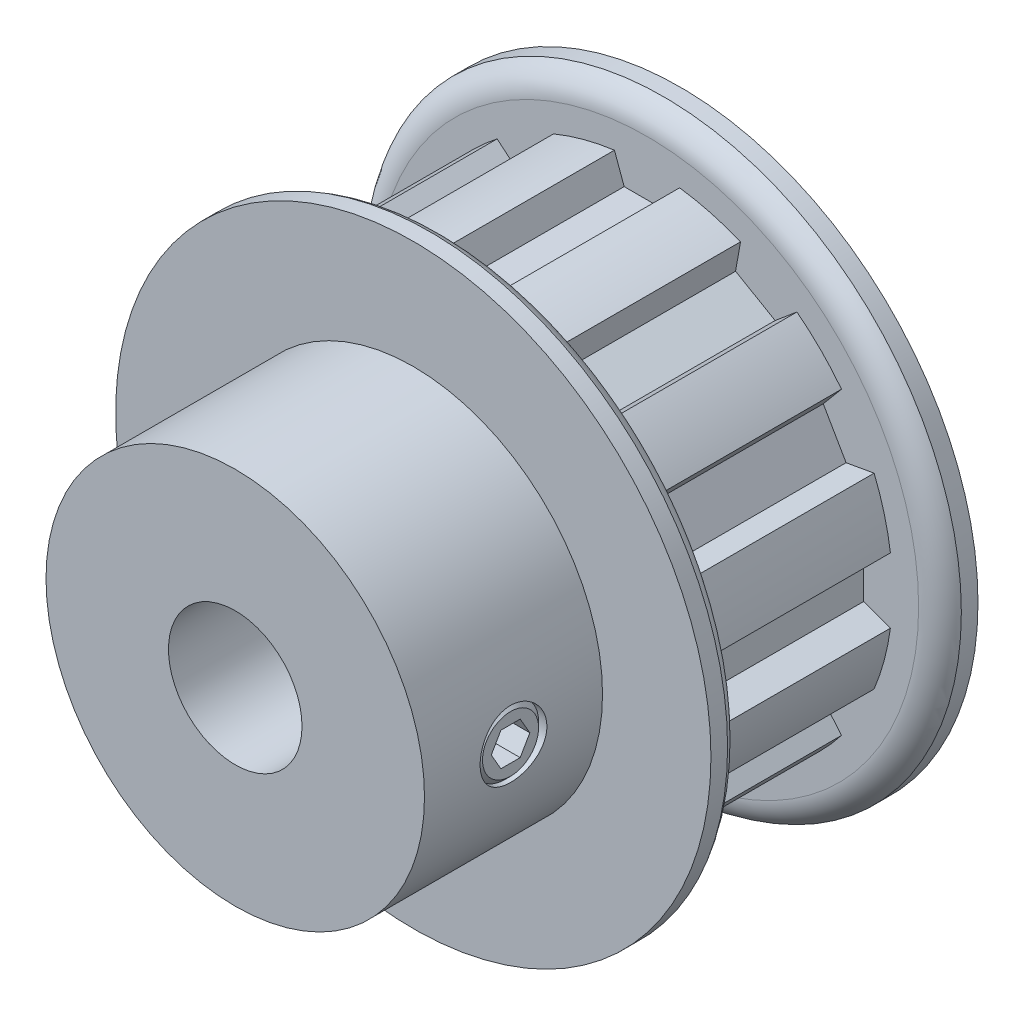
SolidWorks part; units mm, degrees
ref_plane "Front Plane" through (0, 0, 0) normal (0, 0, 1) x (1, 0, 0)
ref_plane "Top Plane" through (0, 0, 0) normal (0, 1, 0) x (1, 0, 0)
ref_plane "Right Plane" through (0, 0, 0) normal (1, 0, 0) x (0, 0, -1)
sketch "Sketch1" plane through (0, 0, 0) normal (0, 0, 1) x (1, 0, 0)
  line L0 (-2.3241, 17.3609) -> (-1.6307, 15.4559)
  line L1 (-1.6307, 15.4559) -> (1.6307, 15.4559)
  line L2 (1.6307, 15.4559) -> (2.3241, 17.3609)
  line L3 (-2.3241, 17.3609) -> (2.3241, 17.3609)
  line L4 (0, 0) -> (0, 15.4559) construction
  line L5 (0, 15.4559) -> (0, 19.0119) construction
  circle A0 centre (0, 0) radius 18.1864 construction
  circle A1 centre (0, 0) radius 21.2344 construction
  circle A2 centre (0, 0) radius 17.5158 construction
  point P6 (0, 17.3609)
  point P11 (0, 18.1864)
  point P13 (0, 21.2344)
  point P14 (0, 17.5158)
  dimension "D1" = 1.651
  dimension "D2" = 0.8255
sketch "Sketch2" plane through (0, 0, 0) normal (1, 0, 0) x (0, 0, -1)
  line L0 (-15.875, 4.7625) -> (15.875, 4.7625)
  line L1 (-15.875, 4.7625) -> (-15.875, 13.5001)
  line L2 (-15.875, 13.5001) -> (-3.175, 13.5001)
  line L3 (-3.175, 13.5001) -> (-3.175, 21.2344)
  line L4 (-3.175, 21.2344) -> (-0.8001, 21.2344) construction
  line L5 (-0.8001, 21.2344) -> (-0.8001, 17.5158) construction
  line L6 (-0.8001, 17.5158) -> (13.5001, 17.5158)
  line L7 (13.5001, 17.5158) -> (13.5001, 21.2344) construction
  line L8 (13.5001, 21.2344) -> (15.875, 21.2344) construction
  line L9 (15.875, 21.2344) -> (15.875, 4.7625)
  line L10 (-15.875, 0) -> (15.875, 0) construction
  line L13 (-3.175, 21.2344) -> (-1.9876, 21.2344)
  line L14 (-0.8001, 19.3751) -> (-0.8001, 17.5158)
  line L15 (13.5001, 17.5158) -> (13.5001, 19.3751)
  line L16 (14.6875, 21.2344) -> (15.875, 21.2344)
  arc A0 (-0.8001, 19.3751) -> (-1.9876, 21.2344) centre (-2.8495, 19.3751) ccw
  arc A1 (13.5001, 19.3751) -> (14.6875, 21.2344) centre (15.5495, 19.3751) cw
  point P12 (-0.8001, 19.3751)
  point P14 (-1.9876, 21.2344)
  point P20 (13.5001, 19.3751)
  point P21 (14.6875, 21.2344)
  point P25 (13.5001, 0)
  point P26 (-0.8001, 0)
  dimension "Bore" = 9.525
  dimension "Hub Dia" = 27.0002
  dimension "Outside Width" = 19.05
  dimension "Inside Width" = 14.3002
revolve "Revolve1" add sketch "Sketch2" angle 360 mid plane about L10
sketch "Sketch3" plane through (0, 0, 0) normal (0, 0, 1) x (1, 0, 0)
  line L0 (-1.6307, 15.4559) -> (1.6307, 15.4559) construction
  line L1 (1.6307, 15.4559) -> (2.3241, 17.3609) construction
  line L2 (-2.3241, 17.3609) -> (-1.6307, 15.4559) construction
  line L3 (-1.6307, 15.4559) -> (1.6307, 15.4559)
  line L4 (1.6307, 15.4559) -> (2.3241, 17.3609)
  line L5 (-2.3241, 17.3609) -> (-1.6307, 15.4559)
  circle A0 centre (0, 0) radius 17.5158 construction
  arc A1 (2.3241, 17.3609) -> (-2.3241, 17.3609) centre (0, 0) ccw
extrude "Cut-Extrude1" cut sketch "Sketch3" against normal up to vertex (13.5001 mm away) from vertex at 0.8001 starting at point (0, 17.5158, 0.8001)
pattern_circular "CirPattern1" count 12 over 360 about axis through (0, 0, 0) along (0, 0, 1) of "Cut-Extrude1"
sketch "Sketch4" plane through (0, 0, 0) normal (1, 0, 0) x (0, -1, 0)
  line L0 (0, -3.175) -> (0, -15.875) construction
  line L1 (-13.5001, -3.175) -> (13.5001, -3.175) construction
  line L2 (-13.5001, -15.875) -> (13.5001, -15.875) construction
  circle A0 centre (0, -9.525) radius 2.3813
  dimension "D1" = 4.7625
extrude "Cut-Extrude2" cut sketch "Sketch4" along normal through all
ref_plane "Plane1" through (0, 0, 9.525) normal (0, 0, 1) x (1, 0, 0)
sketch "Sketch5" plane through (0, 0, 9.525) normal (0, 0, 1) x (1, 0, 0)
  line L0 (0, 0.1664) -> (0, 13.5001) construction
  line L1 (4.7625, -2.0003) -> (4.7625, 0)
  line L2 (5.1435, -2.3813) -> (12.9074, -2.3813)
  line L3 (4.7625, 0) -> (13.5001, 0) construction
  line L4 (4.7625, 0) -> (13.2884, 0)
  line L5 (13.2884, 0) -> (13.2884, -2.0003)
  line L6 (5.1435, -2.3813) -> (4.7625, -2.0003)
  line L7 (13.2884, -2.0003) -> (12.9074, -2.3813)
  circle A0 centre (0, 0) radius 13.5001 construction
  circle A1 centre (0, 0) radius 4.7625 construction
  point P2 (4.7625, -2.3813)
  point P11 (13.2884, -2.3813)
revolve "Revolve2" add sketch "Sketch5" angle 360 mid plane about L4
sketch "Sketch6" plane through (13.2884, 5.3841, 0) normal (-1, 0, 0) x (0, -1, 0)
  line L1 (5.3841, 10.8998) -> (4.1935, 10.2124)
  line L2 (4.1935, 10.2124) -> (4.1935, 8.8376)
  line L3 (4.1935, 8.8376) -> (5.3841, 8.1502)
  line L4 (5.3841, 8.1502) -> (6.5748, 8.8376)
  line L5 (6.5748, 8.8376) -> (6.5748, 10.2124)
  line L6 (6.5748, 10.2124) -> (5.3841, 10.8998)
  circle A0 centre (5.3841, 9.525) radius 1.1906 construction
  dimension "D1" = 2.3813
extrude "Cut-Extrude3" cut sketch "Sketch6" along normal blind 1.7859
equation "\"D2@Sketch1\" = \"D1@Sketch1\"/2"
equation "\"D1@Sketch4\" = \"Bore@Sketch2\"/2"
equation "\"D1@Sketch6\" = \"D1@Sketch4\"/2"
equation "\"D1@Cut-Extrude3\" = \"D1@Sketch6\"*.75"
